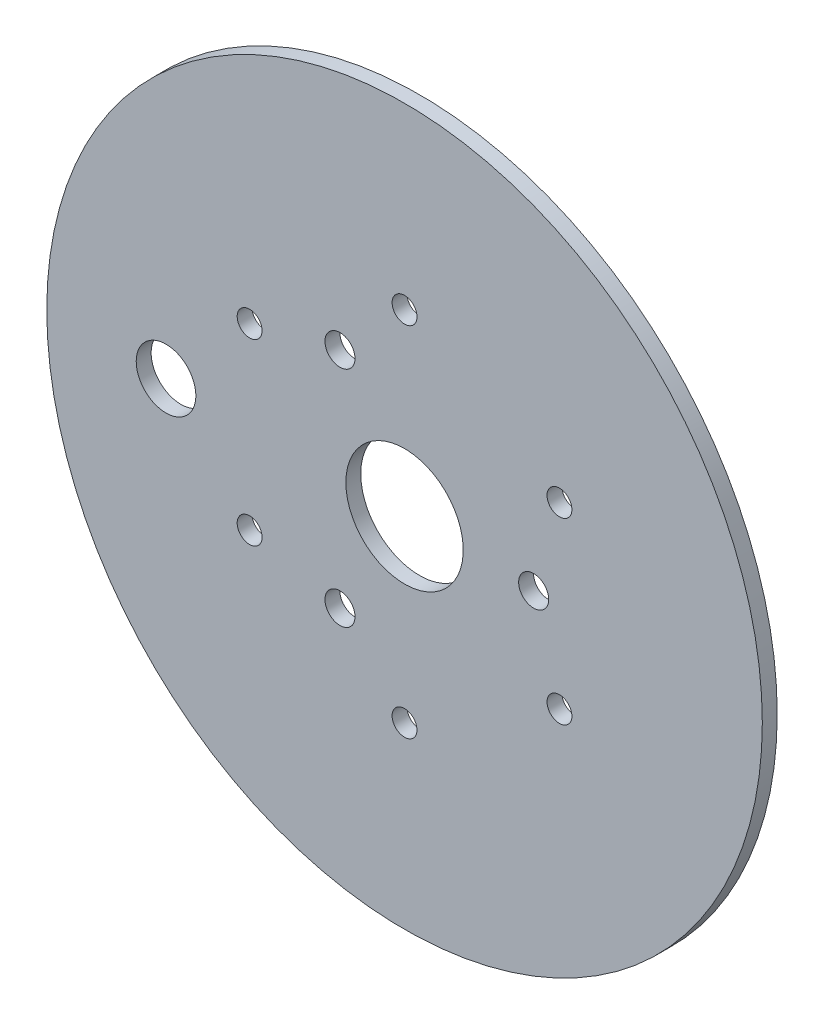
SolidWorks part; units mm, degrees
ref_plane "Front" through (0, 0, 0) normal (0, 0, 1) x (1, 0, 0)
ref_plane "Top" through (0, 0, 0) normal (0, 1, 0) x (1, 0, 0)
ref_plane "Right" through (0, 0, 0) normal (1, 0, 0) x (0, 0, -1)
sketch "Sketch1" plane through (0, 0, 0) normal (0, 0, 1) x (1, 0, 0)
  circle A0 centre (0, 0) radius 76.2
  circle A1 centre (0, 0) radius 38.1 construction
  circle A2 centre (0, 0) radius 27.5 construction
  point P5 (0, 38.1)
  point P6 (0, 27.5)
  dimension "D1" = 76.2
  dimension "D2" = 152.4
  dimension "D3" = 55
extrude "Boss-Extrude1" add sketch "Sketch1" along normal blind 3.175
sketch "Sketch2" plane through (0, 0, 3.175) normal (0, 0, 1) x (1, 0, 0)
  line L0 (0, 0) -> (0, 38.1) construction
  line L1 (0, 0) -> (-13.75, 23.8157) construction
  circle A0 centre (0, 0) radius 38.1 construction
  circle A1 centre (0, 0) radius 27.5 construction
  point P8 (0, 38.1)
  point P9 (-13.75, 23.8157)
  dimension "D1" = 76.2
  dimension "D2" = 55
  dimension "D3" = 30
hole_wizard "M5 Clearance Hole2" positions "3DSketch2" profile "Sketch4" hole size "M5" standard "ANSI Metric"
sketch3d "3DSketch2"
  point P0 (0, 38.1, 3.175)
sketch "Sketch4" plane through (0, 38.1, 3.175) normal (1, 0, 0) x (0, -1, 0)
  line L0 (0, 0) -> (0, 14.0383)
  line L1 (0, 14.0383) -> (2.65, 12.446)
  line L2 (2.65, 12.446) -> (2.65, 0)
  line L5 (2.65, 0) -> (0, 0)
  line L10 (0, 14.0383) -> (-2.65, 12.446) construction
  line L11 (0, -6.35) -> (0, 107.95) construction
  dimension "Hole Dia." = 5.3
  dimension "Hole Depth" = 12.446
  dimension "Drill Angle" = 118
hole_wizard "M6 Clearance Hole1" positions "3DSketch3" profile "Sketch5" hole size "M6" standard "ANSI Metric"
sketch3d "3DSketch3"
  point P0 (-13.75, 23.8157, 3.175)
sketch "Sketch5" plane through (-13.75, 23.8157, 3.175) normal (1, 0, 0) x (0, -1, 0)
  line L0 (0, 0) -> (0, 14.3688)
  line L1 (0, 14.3688) -> (3.2, 12.446)
  line L2 (3.2, 12.446) -> (3.2, 0)
  line L5 (3.2, 0) -> (0, 0)
  line L10 (0, 14.3688) -> (-3.2, 12.446) construction
  line L11 (0, -6.35) -> (0, 107.95) construction
  dimension "Hole Dia." = 6.4
  dimension "Hole Depth" = 12.446
  dimension "Drill Angle" = 118
pattern_circular "CirPattern1" count 3 over 360 about axis through (0, 0, 0) along (0, 0, 1) of "M6 Clearance Hole1"
pattern_circular "CirPattern2" count 6 over 360 about axis through (0, 0, 0) along (0, 0, 1) of "M5 Clearance Hole2"
sketch "Sketch6" plane through (0, 0, 3.175) normal (0, 0, 1) x (1, 0, 0)
  line L0 (0, 0) -> (18.0785, 67.4699) construction
  line L1 (0, 0) -> (0, 52.705) construction
  circle A0 centre (0, 0) radius 50.8 construction
  circle A1 centre (0, 0) radius 69.85 construction
  circle A2 centre (0, 52.705) radius 1.905
  circle A3 centre (17.5855, 65.6298) radius 1.905
  arc A4 (-1.712, 53.5404) -> (17.2993, 67.5132) centre (21.1152, 42.4015) cw
  arc A5 (1.712, 51.8696) -> (17.8717, 63.7465) centre (21.1152, 42.4015) cw
  dimension "D1" = 101.6
  dimension "D2" = 139.7
  dimension "D4" = 3.81
  dimension "D5" = 25.4
  dimension "D3" = 15
extrude "Cut-Extrude1" [suppressed] cut sketch "Sketch6" against normal blind 3.175 contours A2 A5 A3 A4 | A3
pattern_circular "CirPattern3" [suppressed] count 25 every 15
sketch "Sketch7" plane through (0, 0, 0) normal (0, 0, -1) x (-1, 0, 0)
  circle A0 centre (0, 0) radius 12.5
  dimension "D1" = 25
extrude "Cut-Extrude2" cut sketch "Sketch7" against normal through all
sketch "Sketch8" plane through (0, 0, 0) normal (0, 0, -1) x (-1, 0, 0)
  line L0 (50.8, 0) -> (0, 0) construction
  circle A0 centre (0, 0) radius 44.45 construction
  circle A1 centre (50.8, 0) radius 6.35
  dimension "D1" = 88.9
  dimension "D2" = 12.7
extrude "Cut-Extrude3" cut sketch "Sketch8" against normal through all
